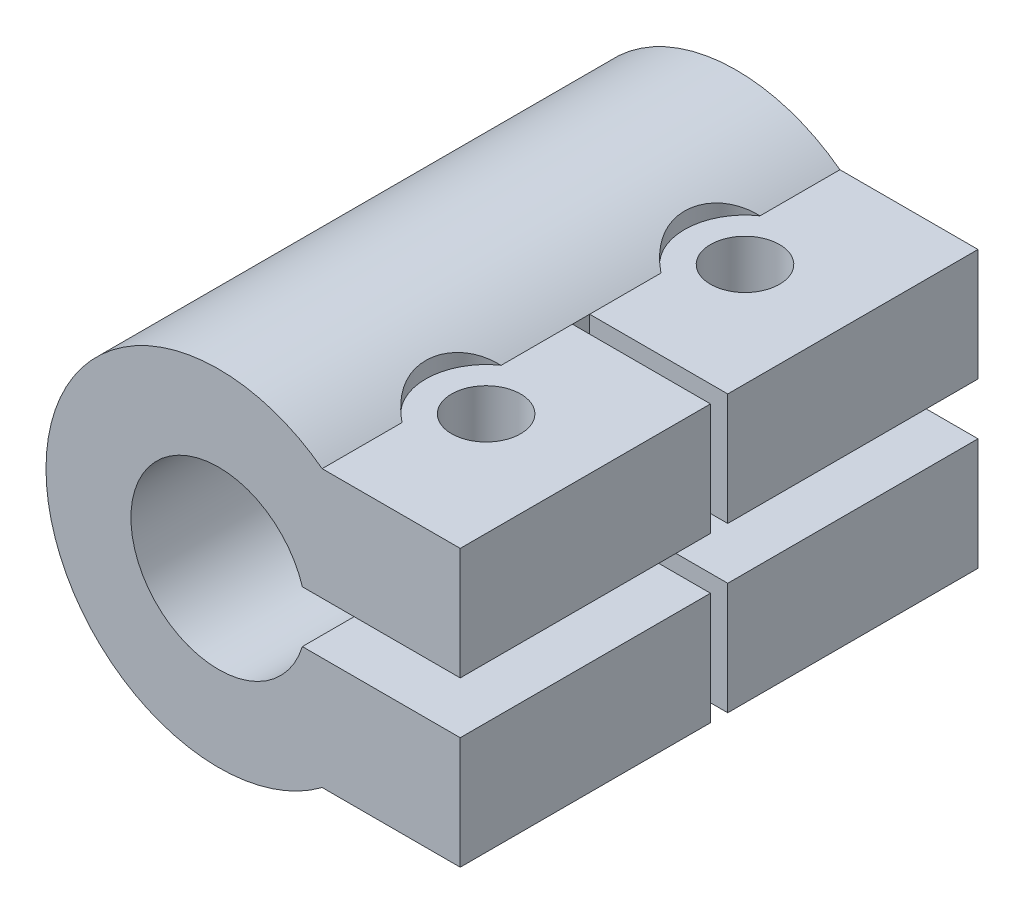
SolidWorks part; units mm, degrees
ref_plane "Front Plane" through (0, 0, 0) normal (0, 0, 1) x (1, 0, 0)
ref_plane "Top Plane" through (0, 0, 0) normal (0, 1, 0) x (1, 0, 0)
ref_plane "Right Plane" through (0, 0, 0) normal (1, 0, 0) x (0, 0, -1)
sketch "Sketch1" plane through (0, 0, 0) normal (0, 0, 1) x (1, 0, 0)
  line L0 (8, 12.2361) -> (8, 7.7639)
  line L1 (16, 18) -> (24, 18)
  line L2 (24, 18) -> (24, 11.5)
  line L3 (12.5981, 8.5) -> (24, 8.5)
  line L6 (24, 8.5) -> (24, 2)
  line L7 (24, 2) -> (16, 2)
  line L8 (24, 11.5) -> (12.5981, 11.5)
  arc A0 (16, 18) -> (16, 2) centre (10, 10) ccw
  arc A1 (8, 7.7639) -> (12.5981, 8.5) centre (10, 10) ccw
  arc A2 (12.5981, 11.5) -> (8, 12.2361) centre (10, 10) ccw
extrude "Boss-Extrude1" add sketch "Sketch1" along normal blind 30
sketch3d "3DSketch1"
  line L0 (24, 18, 0) -> (16, 18, 0) construction
  line L1 (24, 18, 30) -> (24, 18, 0) construction
  line L2 (24, 18, 15) -> (16, 18, 15) construction
  line L3 (16, 18, 30) -> (16, 18, 0) construction
  circle A0 centre (18, 18, 7.5) radius 2
  point P2 (18, 20, 7.5)
  dimension "D1" = 7.5
  dimension "D3" = 4
  dimension "D2" = 6
sketch "Sketch3" plane through (0, 18, 0) normal (0, 1, 0) x (1, 0, 0)
  line L0 (24, -30) -> (24, 0) construction
  line L1 (24, -30) -> (16, -30) construction
  circle A0 centre (18, -22.5) radius 2
  circle A1 centre (18, -22.5) radius 3.5
  point P7 (18, -22.5)
  dimension "D2" = 4
  dimension "D4" = 7
  dimension "D1" = 6
  dimension "D3" = 7.5
extrude "Cut-Extrude2" cut sketch "Sketch3" against normal through all contours A0
sketch "Sketch8" plane through (0, 18, 0) normal (0, 1, 0) x (1, 0, 0)
  circle A0 centre (18, -22.5) radius 3.5
  dimension "D1" = 7
extrude "Cut-Extrude5" cut sketch "Sketch8" along normal blind 10
sketch "Sketch9" plane through (0, 18, 0) normal (0, 1, 0) x (1, 0, 0)
  line L0 (16, -19.6277) -> (16, 0) construction
  line L1 (16, -14.5) -> (24, -14.5)
  line L2 (16, -14.5) -> (16, -15.5)
  line L3 (16, -15.5) -> (24, -15.5)
  line L4 (24, -14.5) -> (24, -15.5)
  line L5 (24, -30) -> (24, 0) construction
  line L6 (24, 0) -> (16, 0) construction
  dimension "D1" = 1
  dimension "D2" = 14.5
extrude "Cut-Extrude6" cut sketch "Sketch9" against normal through all and the other way through all
sketch "Sketch10" plane through (0, 2, 0) normal (0, -1, 0) x (1, 0, 0)
  line L1 (15.068, 20.8824) -> (17.9349, 19.152)
  line L2 (17.9349, 19.152) -> (20.8669, 20.7696)
  line L3 (20.8669, 20.7696) -> (20.932, 24.1176)
  line L4 (20.932, 24.1176) -> (18.0651, 25.848)
  line L5 (18.0651, 25.848) -> (15.1331, 24.2304)
  line L6 (15.1331, 24.2304) -> (15.068, 20.8824)
  line L7 (16, 22.5) -> (16, 15.5) construction
  circle A0 centre (18, 22.5) radius 2.9 construction
  point P0 (18, 22.5)
  dimension "D1" = 2.9
  dimension "D2" = 1.9349
extrude "Cut-Extrude7" cut sketch "Sketch10" against normal blind 3 and the other way through all
sketch "Sketch11" plane through (0, 2, 0) normal (0, -1, 0) x (1, 0, 0)
  line L0 (16, 15) -> (28.6849, 15) construction
ref_plane "Plane1" through (0, 0, 15) normal (0, 0, 1) x (1, 0, 0)
mirror "Mirror1" about plane through (0, 0, 15) normal (0, 0, 1) of "Cut-Extrude7"
mirror "Mirror2" about plane through (0, 0, 15) normal (0, 0, 1) of "Cut-Extrude5", "Cut-Extrude2"
sketch "Sketch12" plane through (0, 0, 30) normal (0, 0, 1) x (1, 0, 0)
  circle A0 centre (10, 10) radius 5.08
  dimension "D1" = 10.16
extrude "Cut-Extrude8" cut sketch "Sketch12" against normal blind 15
